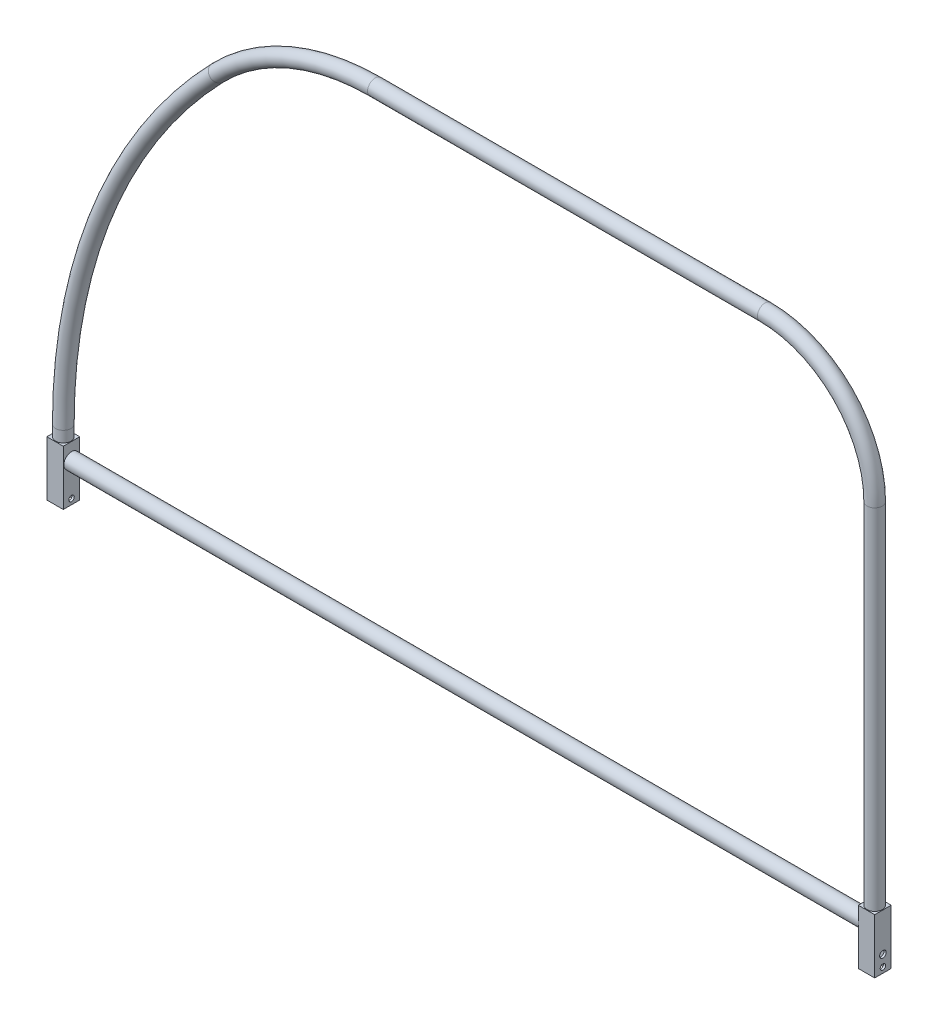
SolidWorks part; units mm, degrees
material "6061 Alloy"
ref_plane "Front Plane" through (0, 0, 0) normal (0, 0, 1) x (1, 0, 0)
ref_plane "Top Plane" through (0, 0, 0) normal (0, 1, 0) x (1, 0, 0)
ref_plane "Right Plane" through (0, 0, 0) normal (1, 0, 0) x (0, 0, -1)
other "Configuration Table"
sketch "Sketch80" plane through (0, 0, 0) normal (0, 0, 1) x (1, 0, 0)
  line L0 (0, 0) -> (0, 12.7)
  line L1 (361.3263, 531.773) -> (812.8, 531.773)
  line L2 (939.8, 404.773) -> (939.8, -14.327)
  arc A0 (0, 12.7) -> (178.8772, 454.4884) centre (635, 12.7) cw
  arc A1 (178.8772, 454.4884) -> (361.3263, 531.773) centre (361.3263, 277.773) cw
  arc A2 (812.8, 531.773) -> (939.8, 404.773) centre (812.8, 404.773) cw
  dimension "D3" = 635
  dimension "D4" = 254
  dimension "D5" = 127
  dimension "D1" = 546.1
  dimension "D2" = 12.7
  dimension "D6" = 939.8
sweep "Sweep1" add path "Sketch80" circular profile diameter 17.78 parameters "D3"=17.78
sketch "Sketch107" plane through (0, 0, 0) normal (0, -1, 0) x (1, 0, 0)
  line L1 (9.525, 9.525) -> (-9.525, 9.525)
  line L2 (9.525, 9.525) -> (9.525, -9.525)
  line L3 (9.525, -9.525) -> (-9.525, -9.525)
  line L4 (-9.525, 9.525) -> (-9.525, -9.525)
  line L5 (9.525, 9.525) -> (-9.525, -9.525) construction
  line L6 (9.525, -9.525) -> (-9.525, 9.525) construction
  line L7 (949.325, 9.525) -> (930.275, 9.525)
  line L8 (949.325, 9.525) -> (949.325, -9.525)
  line L9 (949.325, -9.525) -> (930.275, -9.525)
  line L10 (930.275, 9.525) -> (930.275, -9.525)
  line L11 (949.325, 9.525) -> (930.275, -9.525) construction
  line L12 (949.325, -9.525) -> (930.275, 9.525) construction
  point P0 (0, 0)
  point P6 (939.8, 0)
  dimension "D1" = 19.05
  dimension "D2" = 19.05
extrude "Boss-Extrude1" add sketch "Sketch107" along normal blind 63.5
sketch "Sketch108" plane through (0, 0, 0) normal (0, 0, 1) x (1, 0, 0)
  line L0 (9.525, -19.05) -> (930.275, -19.05)
  line L1 (9.525, -63.5) -> (9.525, 0) construction
  line L2 (930.275, -63.5) -> (930.275, 0) construction
  dimension "D1" = 19.05
sweep "Sweep3" add path "Sketch108" circular profile diameter 17.78 parameters "D3"=17.78
shell "Shell17" thickness 2.54
sketch "Sketch115" plane through (-9.525, 0, 0) normal (-1, 0, 0) x (0, 0, 1)
  line L0 (9.525, -63.5) -> (-9.525, -63.5) construction
  circle A0 centre (0, -57.15) radius 3.175
  dimension "D2" = 6.35
  dimension "D1" = 6.35
extrude "Cut-Extrude1" cut sketch "Sketch115" against normal through all
sketch "Sketch116" plane through (9.525, 0, 0) normal (1, 0, 0) x (0, 0, -1)
  line L0 (9.525, -63.5) -> (-9.525, -63.5) construction
  circle A0 centre (0, -44.45) radius 3.81
  dimension "D2" = 7.62
  dimension "D1" = 19.05
sketch "Sketch119" plane through (949.325, 0, 0) normal (1, 0, 0) x (0, 0, -1)
  circle A0 centre (0, -44.45) radius 3.81
  dimension "D1" = 7.62
sketch "Sketch120" plane through (-9.525, 0, 0) normal (-1, 0, 0) x (0, 0, 1)
  circle A0 centre (0, -44.45) radius 3.81
  dimension "D1" = 7.62
extrude "Cut-Extrude2" cut sketch "Sketch119" against normal blind 2.54
extrude "Cut-Extrude3" cut sketch "Sketch120" against normal blind 2.54
equation "\"A\"= 3"
equation "\"B\"= 1"
